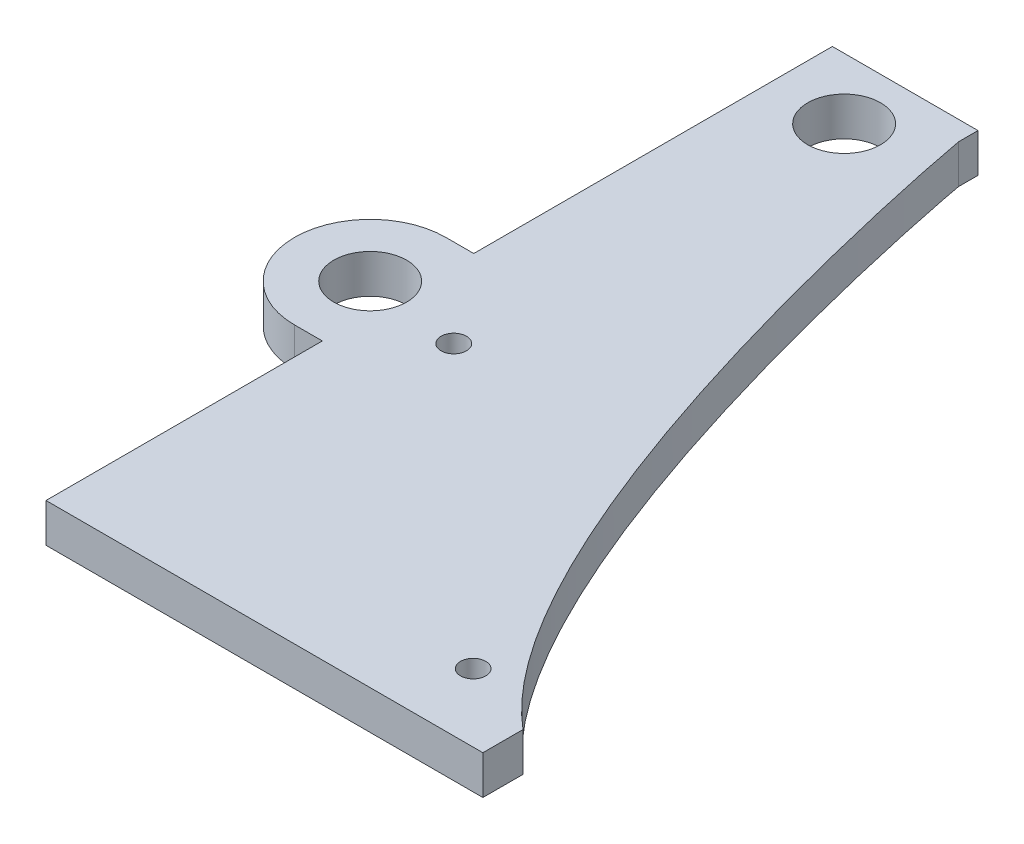
SolidWorks part; units mm, degrees
ref_plane "Front Plane" through (0, 0, 0) normal (0, 0, 1) x (1, 0, 0)
ref_plane "Top Plane" through (0, 0, 0) normal (0, 1, 0) x (1, 0, 0)
ref_plane "Right Plane" through (0, 0, 0) normal (1, 0, 0) x (0, 0, -1)
sketch "Sketch1" plane through (0, 0, 0) normal (0, 1, 0) x (1, 0, 0)
  line L0 (9.525, -53.975) -> (60.325, -53.975) construction
  line L1 (-9.525, -53.975) -> (9.525, -53.975) construction
  line L2 (-9.525, -53.975) -> (-9.525, 53.975) construction
  line L3 (-9.525, 53.975) -> (9.525, 53.975)
  line L4 (9.525, -53.975) -> (9.525, 53.975) construction
  line L5 (-9.525, -53.975) -> (9.525, 53.975) construction
  line L6 (-9.525, 53.975) -> (9.525, -53.975) construction
  line L7 (0, 53.975) -> (0, 45.9867) construction
  line L8 (-9.525, 50.7492) -> (9.525, 50.7492) construction
  line L9 (9.525, 51.435) -> (9.525, 53.975)
  line L10 (60.325, -53.975) -> (60.325, -48.895) construction
  line L11 (60.325, -48.895) -> (-9.525, -48.895) construction
  line L12 (60.325, -53.975) -> (60.325, -48.895) construction
  line L13 (60.325, -48.895) -> (-9.525, -48.895)
  line L14 (-9.525, -48.895) -> (-9.525, 53.975)
  line L15 (31.115, -19.685) -> (31.115, -48.895) construction
  circle A0 centre (0, 45.9867) radius 4.7625
  spline S0 degree 3 poles (9.525, 51.435) (9.525, 51.2145) (27.8191, -48.895) (60.325, -48.895) knots 0 0 0 0 1 1 1 1
  point P4 (0, 0)
  dimension "D5" = 9.525
  dimension "D1" = 107.95
  dimension "D2" = 19.05
  dimension "D3" = 50.8
  dimension "D4" = 2.54
  dimension "D6" = 104.7242
  dimension "D7" = 5.08
  dimension "D8" = 40.64
  dimension "D9" = 29.21
extrude "Boss-Extrude1" add sketch "Sketch1" along normal blind 5.08
sketch "Sketch4" plane through (0, 5.08, 0) normal (0, 1, 0) x (1, 0, 0)
  line L0 (-9.525, 53.975) -> (-9.525, -48.895) construction
  line L1 (60.325, -48.895) -> (41.275, -48.895)
  line L2 (60.325, -48.895) -> (60.325, -53.975)
  line L3 (60.325, -53.975) -> (41.275, -53.975)
  line L4 (41.275, -48.895) -> (41.275, -53.975)
  line L5 (60.325, -48.895) -> (41.275, -53.975) construction
  line L6 (60.325, -53.975) -> (41.275, -48.895) construction
  point P4 (50.8, -51.435)
  dimension "D1" = 50.8
  dimension "D2" = 5.08
extrude "Boss-Extrude2" add sketch "Sketch4" against normal up to surface (5.08 mm away) up to face at (17.145, 0, -2.286)
sketch "Sketch5" plane through (0, 0, 0) normal (0, -1, 0) x (1, 0, 0)
  circle A4 centre (-0.635, 4.445) radius 1.6607
  circle A5 centre (37.465, 40.005) radius 1.651
extrude "Cut-Extrude1" cut sketch "Sketch5" against normal through all both
sketch "Sketch6" plane through (0, 0, 0) normal (0, -1, 0) x (1, 0, 0)
  line L0 (-9.525, 2.8423) -> (-13.1707, 2.8423) construction
  line L1 (-9.525, -53.975) -> (-9.525, 48.895) construction
  line L2 (-13.1707, 12.7483) -> (-9.525, 12.7483)
  line L3 (-13.1707, -7.0637) -> (-9.525, -7.0637)
  line L4 (-9.525, 12.7483) -> (-9.525, 12.053)
  line L5 (-9.525, -7.0637) -> (-9.525, -6.3685)
  line L6 (41.275, 53.975) -> (60.325, 53.975) construction
  circle A0 centre (-13.1707, 2.8423) radius 4.7625
  arc A1 (-9.525, -6.3685) -> (-9.525, 12.053) centre (-13.1707, 2.8423) ccw
  arc A2 (-13.1707, 12.7483) -> (-13.1707, -7.0637) centre (-13.1707, 2.8423) ccw
  dimension "D1" = 9.525
  dimension "D3" = 19.812
  dimension "D2" = 3.6457
  dimension "D4" = 51.1327
extrude "Boss-Extrude3" add sketch "Sketch6" against normal blind 5.08
sketch "Sketch8" plane through (0, 5.08, 0) normal (0, 1, 0) x (1, 0, 0)
  circle A0 centre (-13.1707, -2.8423) radius 4.7625
extrude "Cut-Extrude2" cut sketch "Sketch8" against normal through all
sketch "Sketch9" plane through (0, 0, 0) normal (0, -1, 0) x (1, 0, 0)
  line L0 (41.275, 48.895) -> (41.275, 53.975) construction
  line L1 (60.325, 53.975) -> (60.325, 48.895) construction
  line L2 (41.275, 53.975) -> (60.325, 53.975) construction
  line L3 (41.275, 48.895) -> (41.275, 53.975)
  line L4 (60.325, 53.975) -> (60.325, 48.895)
  line L5 (41.275, 53.975) -> (60.325, 53.975)
  line L6 (41.275, 48.895) -> (60.325, 48.895)
extrude "Cut-Extrude3" cut sketch "Sketch9" against normal through all both and the other way through all
sketch "Sketch10" plane through (0, 0, 0) normal (0, -1, 0) x (1, 0, 0)
  line L0 (-9.525, 48.895) -> (60.325, 48.895) construction
  line L1 (-9.525, 48.895) -> (60.325, 48.895) construction
  line L2 (47.625, 43.6465) -> (47.625, 48.895)
  line L3 (47.625, 48.895) -> (60.325, 48.895)
  spline S0 degree 3 poles (403.6577, -2926.3388) (28.4253, 3438.6609) (-194.6007, -3446.0355) (275.8334, 2936.2968) knots -2.047356 -2.047356 -2.047356 -2.047356 3.051792 3.051792 3.051792 3.051792 only from (60.325, 48.895) to (9.525, -51.435) construction
  spline S1 degree 3 poles (60.325, 48.895) (55.8144, 48.895) (51.5774, 46.9674) (47.625, 43.6465) knots 0 0 0 0 0.138763 0.138763 0.138763 0.138763
  dimension "D1" = 12.7
extrude "Cut-Extrude4" cut sketch "Sketch10" against normal through all both
